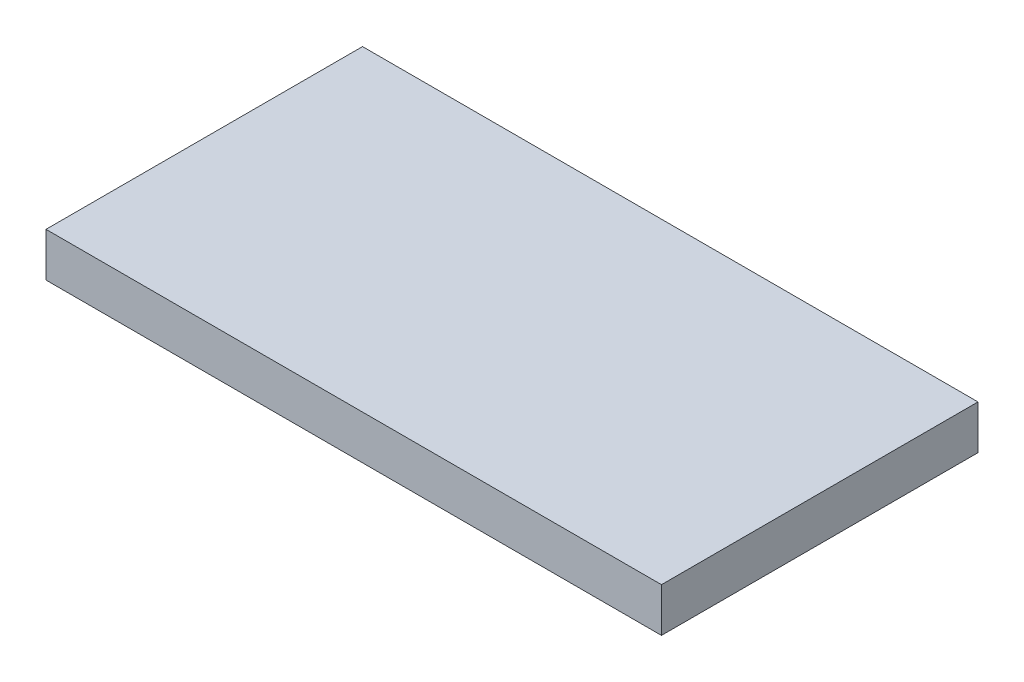
SolidWorks part; units mm, degrees
ref_plane "Front Plane" through (0, 0, 0) normal (0, 0, 1) x (1, 0, 0)
ref_plane "Top Plane" through (0, 0, 0) normal (0, 1, 0) x (1, 0, 0)
ref_plane "Right Plane" through (0, 0, 0) normal (1, 0, 0) x (0, 0, -1)
sketch "Sketch1" plane through (0, 0, 0) normal (0, 1, 0) x (1, 0, 0)
  line L1 (-22.225, -11.43) -> (22.225, -11.43)
  line L2 (-22.225, -11.43) -> (-22.225, 11.43)
  line L3 (-22.225, 11.43) -> (22.225, 11.43)
  line L4 (22.225, -11.43) -> (22.225, 11.43)
  line L5 (-22.225, -11.43) -> (22.225, 11.43) construction
  line L6 (-22.225, 11.43) -> (22.225, -11.43) construction
  point P0 (0, 0)
  dimension "D1" = 22.86
  dimension "D2" = 44.45
extrude "Boss-Extrude1" add sketch "Sketch1" along normal mid plane 3.175
